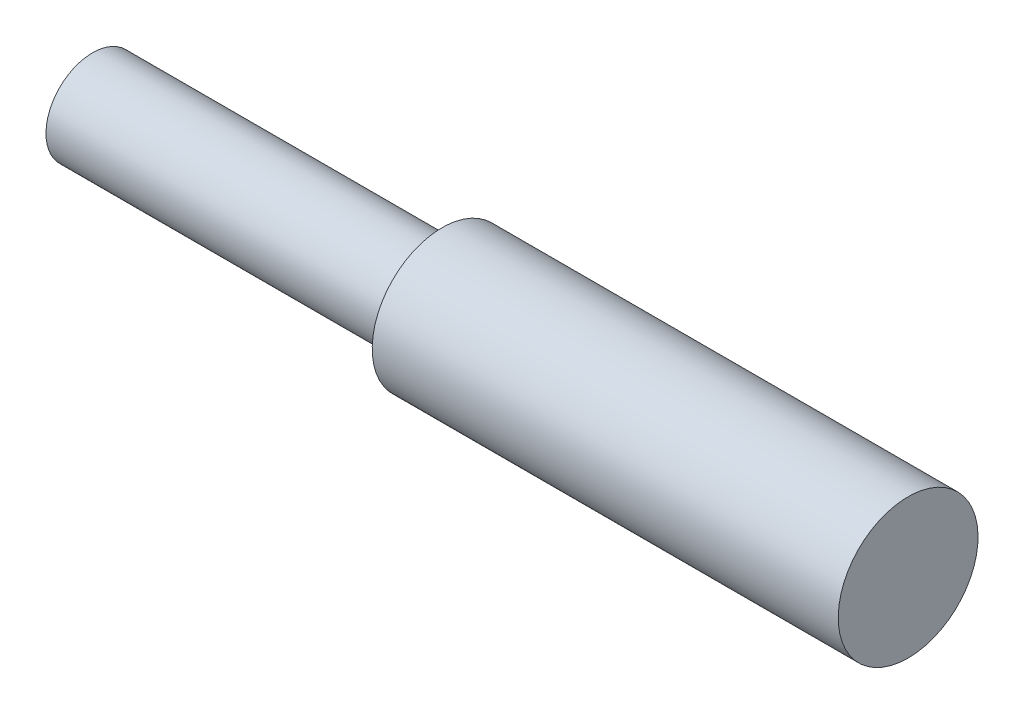
SolidWorks part; units mm, degrees
ref_plane "Front Plane" through (0, 0, 0) normal (0, 0, 1) x (1, 0, 0)
ref_plane "Top Plane" through (0, 0, 0) normal (0, 1, 0) x (1, 0, 0)
ref_plane "Right Plane" through (0, 0, 0) normal (1, 0, 0) x (0, 0, -1)
ref_plane "Plane1" through (0, 0, 0) normal (0, 0, -1) x (-1, 0, 0)
sketch "Sketch1" plane through (0, 0, 0) normal (0, 0, -1) x (-1, 0, 0)
  line L0 (-20, 3) -> (-20, 0)
  line L1 (-20, 0) -> (15, 0)
  line L2 (15, 0) -> (15, 2)
  line L3 (15, 2) -> (0, 2)
  line L4 (0, 2) -> (0, 3)
  line L5 (0, 3) -> (-20, 3)
  line L6 (-20, 0) -> (15, 0) construction
revolve "Revolve1" add sketch "Sketch1" angle 360 about L6
